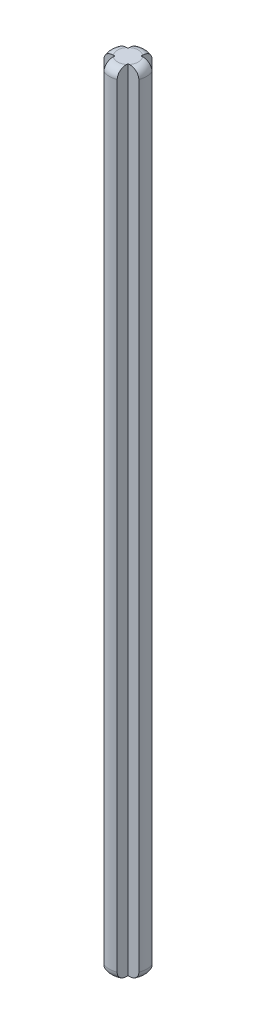
SolidWorks part; units mm, degrees
ref_plane "Front Plane" through (0, 0, 0) normal (0, 0, 1) x (1, 0, 0)
ref_plane "Top Plane" through (0, 0, 0) normal (0, 1, 0) x (1, 0, 0)
ref_plane "Right Plane" through (0, 0, 0) normal (1, 0, 0) x (0, 0, -1)
sketch "Sketch1" plane through (0, 0, 0) normal (0, 1, 0) x (1, 0, 0)
  line L0 (-0.8, -0.8) -> (-0.8, -2.103)
  line L1 (-0.8, 0.8) -> (-2.103, 0.8)
  line L2 (2.103, 0.8) -> (0.8, 0.8)
  line L3 (2.103, -0.8) -> (0.8, -0.8)
  line L4 (0.8, -0.8) -> (0.8, -2.103)
  line L5 (-0.8, -0.8) -> (-2.103, -0.8)
  line L6 (-7.75, 0) -> (-7.75, 0)
  line L7 (-7.75, 0) -> (-7.75, 0)
  line L8 (-0.8, 2.103) -> (-0.8, 0.8)
  line L9 (0.8, 2.103) -> (0.8, 0.8)
  line L10 (-7.75, 0) -> (-7.75, 0)
  line L11 (7.75, 0) -> (7.75, 0)
  line L12 (7.75, 0) -> (7.75, 0)
  line L13 (7.75, 0) -> (7.75, 0)
  line L14 (7.75, 0) -> (7.75, 0)
  line L15 (-7.75, 0) -> (-7.75, 0)
  line L16 (-8.6621, 8.6621) -> (-8.6621, 8.6621)
  line L17 (-8.6621, -8.6621) -> (-8.6621, -8.6621)
  line L18 (-8.6621, -8.6621) -> (-8.6621, -8.6621)
  line L19 (8.6621, -8.6621) -> (8.6621, -8.6621)
  line L20 (8.6621, -8.6621) -> (8.6621, -8.6621)
  line L21 (8.6621, 8.6621) -> (8.6621, 8.6621)
  line L22 (8.6621, 8.6621) -> (8.6621, 8.6621)
  line L23 (-8.6621, 8.6621) -> (-8.6621, 8.6621)
  arc A0 (-2.103, 0.8) -> (-2.103, -0.8) centre (0, 0) ccw
  arc A1 (0.8, 2.103) -> (-0.8, 2.103) centre (0, 0) ccw
  arc A2 (2.103, -0.8) -> (2.103, 0.8) centre (0, 0) ccw
  arc A3 (-0.8, -2.103) -> (0.8, -2.103) centre (0, 0) ccw
  arc A4 (-7.75, 0) -> (-7.75, 0) centre (-7.75, 0) ccw
  arc A5 (-7.75, 0) -> (7.75, 0) centre (0, 0) ccw
  arc A6 (7.75, 0) -> (7.75, 0) centre (7.75, 0) ccw
  arc A7 (7.75, 0) -> (-7.75, 0) centre (0, 0) ccw
  arc A8 (-8.6621, 8.6621) -> (-8.6621, -8.6621) centre (0, 0) ccw
  arc A9 (-8.6621, -8.6621) -> (8.6621, -8.6621) centre (0, 0) ccw
  arc A10 (8.6621, -8.6621) -> (8.6621, 8.6621) centre (0, 0) ccw
  arc A11 (8.6621, 8.6621) -> (-8.6621, 8.6621) centre (0, 0) ccw
  point P26 (0.8, 0)
  dimension "D1" = 4.5
  dimension "D2" = 10
  dimension "D3" = 10
extrude "Boss-Extrude1" add sketch "Sketch1" along normal offset from surface (95.2 mm away) 95.2 contours L0 A3 L4 L3 A2 L2 L9 A1 L8 L1 A0 L5 up to plane "Top Plane"
fillet "Fillet1" radius 1 1 edges at (-2.25, 0, 0)
fillet "Fillet2" radius 1 1 edges at (0, 0, 2.25)
fillet "Fillet3" radius 1 1 edges at (2.25, 0, 0)
fillet "Fillet4" radius 1 1 edges at (0, 0, -2.25)
fillet "Fillet20" radius 1 1 edges at (2.25, 95.2, 0)
fillet "Fillet21" radius 1 1 edges at (0, 95.2, 2.25)
fillet "Fillet22" radius 1 1 edges at (-2.25, 95.2, 0)
fillet "Fillet23" radius 1 1 edges at (0, 95.2, -2.25)
